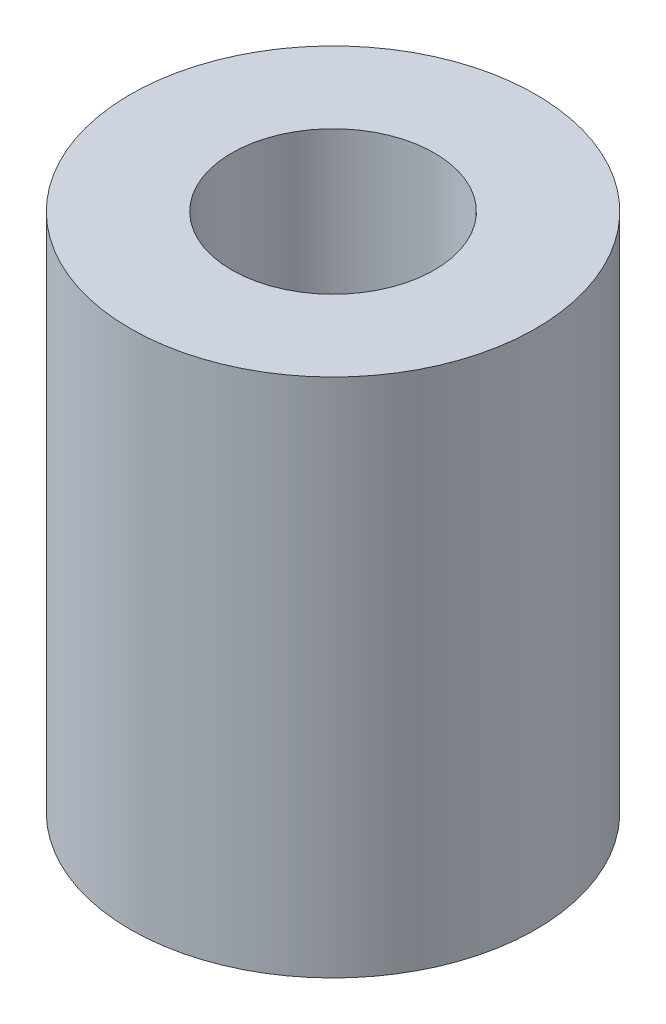
SolidWorks part; units mm, degrees
ref_plane "Front Plane" through (0, 0, 0) normal (0, 0, 1) x (1, 0, 0)
ref_plane "Top Plane" through (0, 0, 0) normal (0, 1, 0) x (1, 0, 0)
ref_plane "Right Plane" through (0, 0, 0) normal (1, 0, 0) x (0, 0, -1)
sketch "Sketch1" plane through (0, 0, 0) normal (0, 1, 0) x (1, 0, 0)
  circle A0 centre (0, 0) radius 3
  circle A1 centre (0, 0) radius 1.5
  dimension "D1" = 6
  dimension "D2" = 3
extrude "Boss-Extrude1" add sketch "Sketch1" along normal blind 7.7
